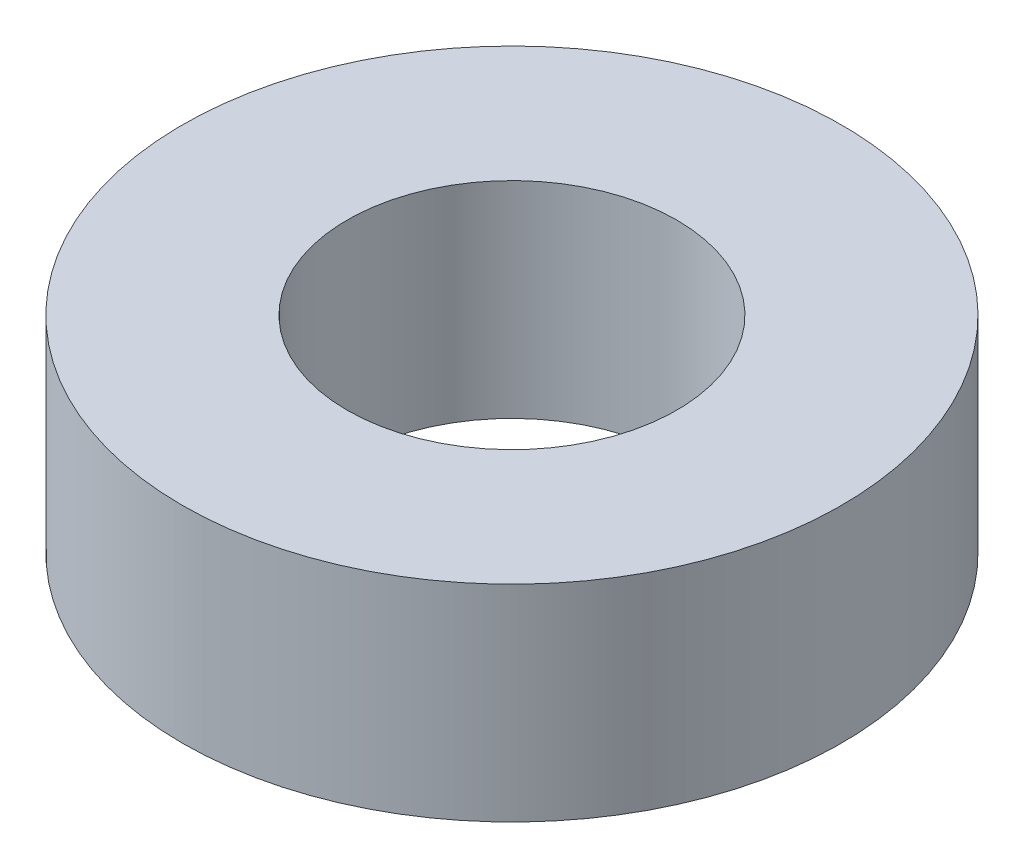
SolidWorks part; units mm, degrees
material "Cast Alloy Steel"
ref_plane "Front Plane" through (0, 0, 0) normal (0, 0, 1) x (1, 0, 0)
ref_plane "Top Plane" through (0, 0, 0) normal (0, 1, 0) x (1, 0, 0)
ref_plane "Right Plane" through (0, 0, 0) normal (1, 0, 0) x (0, 0, -1)
sketch "Sketch1" plane through (0, 0, 0) normal (0, 1, 0) x (1, 0, 0)
  circle A0 centre (0, 0) radius 4
  circle A1 centre (0, 0) radius 8
  dimension "D1" = 8
  dimension "D2" = 16
extrude "Boss-Extrude1" add sketch "Sketch1" along normal blind 5
